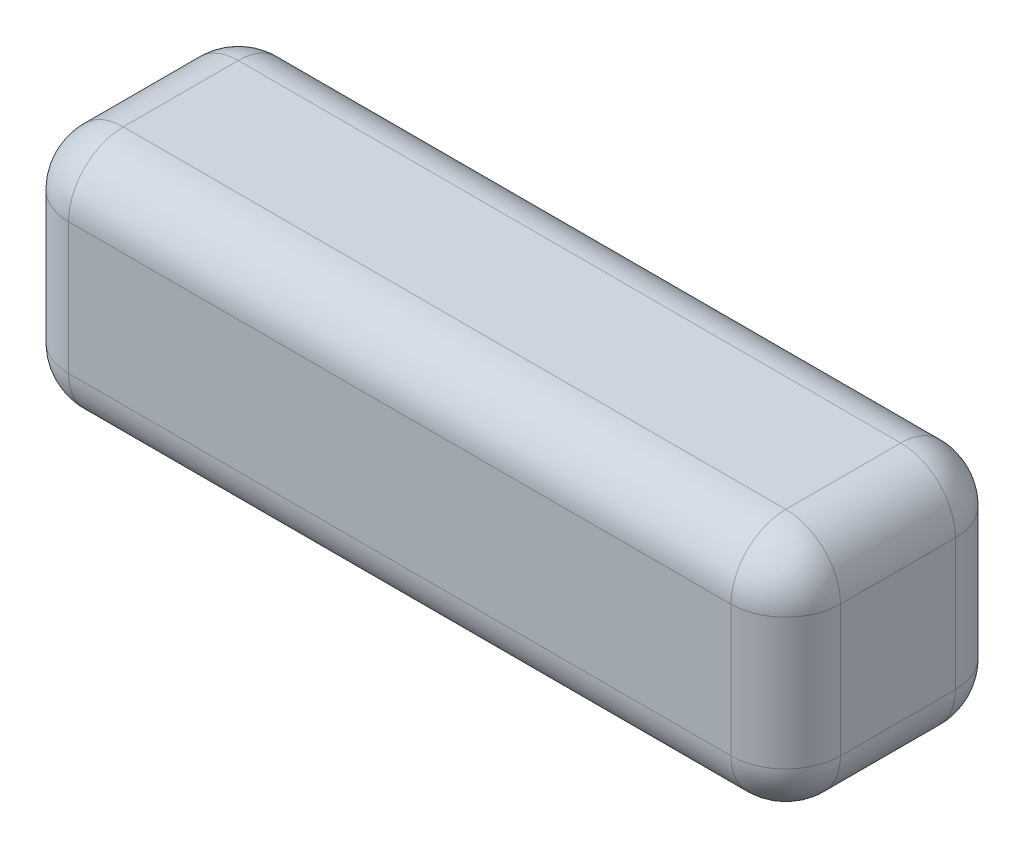
SolidWorks part; units mm, degrees
ref_plane "Front Plane" through (0, 0, 0) normal (0, 0, 1) x (1, 0, 0)
ref_plane "Top Plane" through (0, 0, 0) normal (0, 1, 0) x (1, 0, 0)
ref_plane "Right Plane" through (0, 0, 0) normal (1, 0, 0) x (0, 0, -1)
sketch "Sketch1" plane through (0, 0, 0) normal (0, 1, 0) x (1, 0, 0)
  line L0 (0, 0) -> (0, 20.5) construction
  line L1 (-70.5, 20.5) -> (70.5, 20.5)
  line L2 (-70.5, 20.5) -> (-70.5, -20.5)
  line L3 (-70.5, -20.5) -> (70.5, -20.5)
  line L4 (70.5, 20.5) -> (70.5, -20.5)
  line L5 (0, 0) -> (70.5, 0) construction
  dimension "D1" = 141
  dimension "D2" = 41
extrude "Boss-Extrude1" add sketch "Sketch1" along normal blind 44
fillet "Fillet1" radius 10 12 edges at (-70.5, 22, 20.5) (70.5, 22, 20.5) (70.5, 22, -20.5) (-70.5, 22, -20.5) (0, 44, -20.5) (70.5, 44, 0) (0, 44, 20.5) (-70.5, 44, 0) (0, 0, -20.5) (70.5, 0, 0) (0, 0, 20.5) (-70.5, 0, 0)
